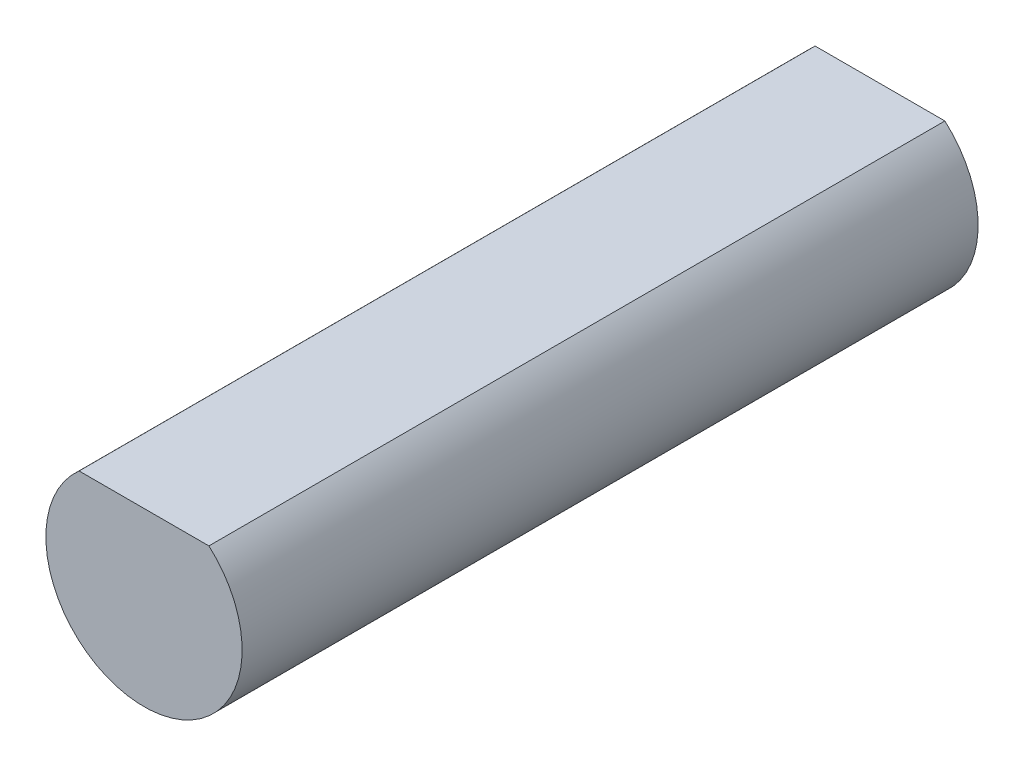
SolidWorks part; units mm, degrees
ref_plane "Front Plane" through (0, 0, 0) normal (0, 0, 1) x (1, 0, 0)
ref_plane "Top Plane" through (0, 0, 0) normal (0, 1, 0) x (1, 0, 0)
ref_plane "Right Plane" through (0, 0, 0) normal (1, 0, 0) x (0, 0, -1)
sketch "Sketch1" plane through (0, 0, 0) normal (0, 0, 1) x (1, 0, 0)
  line L0 (-1.3229, 1.5) -> (1.3229, 1.5)
  arc A0 (1.3229, 1.5) -> (-1.3229, 1.5) centre (0, 0) cw
  point P4 (-7.8238, 1.3297)
  dimension "D1" = 2
  dimension "D2" = 1.5
extrude "Boss-Extrude1" add sketch "Sketch1" along normal blind 15
